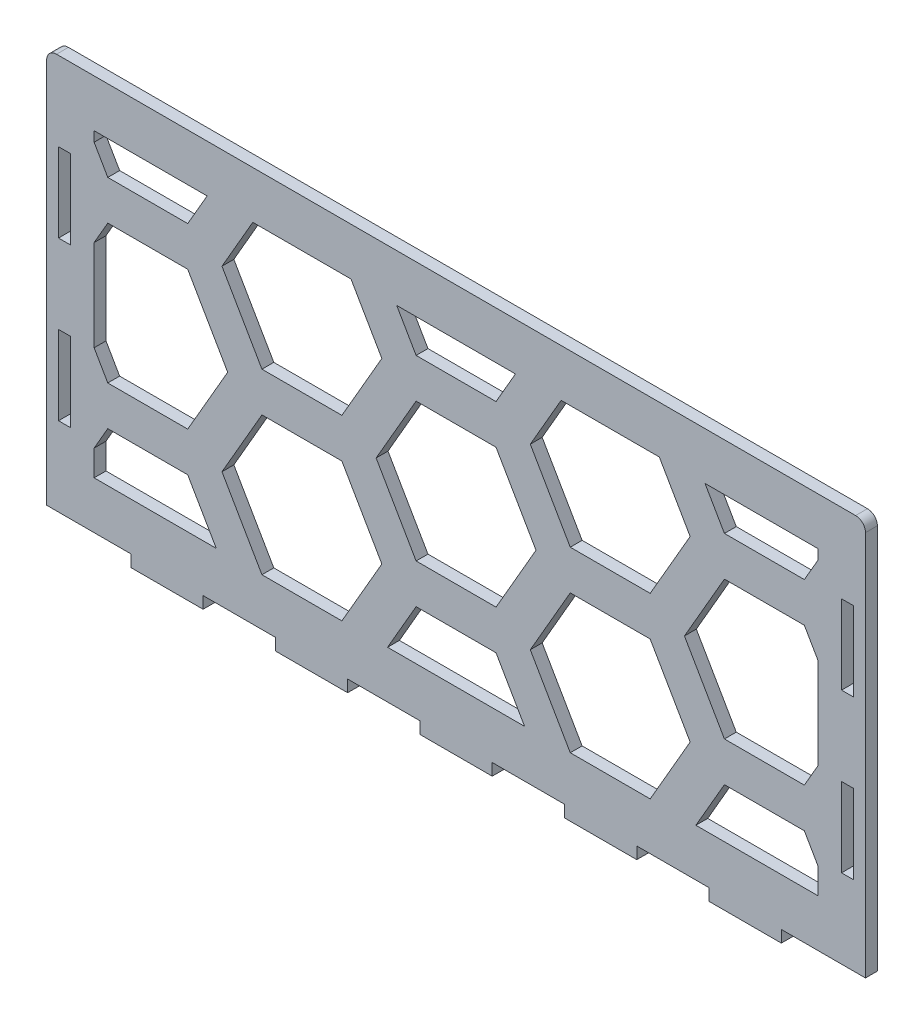
SolidWorks part; units mm, degrees
ref_plane "Front Plane" through (0, 0, 0) normal (0, 0, 1) x (1, 0, 0)
ref_plane "Top Plane" through (0, 0, 0) normal (0, 1, 0) x (1, 0, 0)
ref_plane "Right Plane" through (0, 0, 0) normal (1, 0, 0) x (0, 0, -1)
sketch "Sketch1" plane through (0, 0, 0) normal (0, 0, 1) x (1, 0, 0)
  line L0 (-100.5, -70) -> (-100.5, 70) construction
  line L1 (-103.5, -70) -> (103.5, -70)
  line L2 (-103.5, -70) -> (-103.5, 70)
  line L3 (-103.5, 70) -> (103.5, 70)
  line L4 (103.5, -70) -> (103.5, 70)
  line L5 (-103.5, -70) -> (103.5, 70) construction
  line L6 (-103.5, 70) -> (103.5, -70) construction
  line L7 (100.5, -70) -> (100.5, 70) construction
  line L8 (-63.9545, -73) -> (-45.6818, -73) construction
  line L9 (-9.1364, -73) -> (9.1364, -73)
  line L10 (-9.1364, -73) -> (-9.1364, -70)
  line L11 (-9.1364, -70) -> (9.1364, -70)
  line L12 (9.1364, -73) -> (9.1364, -70)
  line L13 (-9.1364, -73) -> (9.1364, -70) construction
  line L14 (-9.1364, -70) -> (9.1364, -73) construction
  line L15 (27.4091, -73) -> (45.6818, -73)
  line L16 (27.4091, -73) -> (27.4091, -70)
  line L17 (27.4091, -70) -> (45.6818, -70)
  line L18 (45.6818, -73) -> (45.6818, -70)
  line L19 (27.4091, -73) -> (45.6818, -70) construction
  line L20 (27.4091, -70) -> (45.6818, -73) construction
  line L21 (63.9545, -73) -> (82.2273, -73)
  line L22 (63.9545, -73) -> (63.9545, -70)
  line L23 (63.9545, -70) -> (82.2273, -70)
  line L24 (82.2273, -73) -> (82.2273, -70)
  line L25 (63.9545, -73) -> (82.2273, -70) construction
  line L26 (63.9545, -70) -> (82.2273, -73) construction
  line L27 (-45.6818, -73) -> (-27.4091, -73)
  line L28 (-45.6818, -73) -> (-45.6818, -70)
  line L29 (-45.6818, -70) -> (-27.4091, -70)
  line L30 (-27.4091, -73) -> (-27.4091, -70)
  line L31 (-45.6818, -73) -> (-27.4091, -70) construction
  line L32 (-45.6818, -70) -> (-27.4091, -73) construction
  line L33 (-82.2273, -73) -> (-63.9545, -73)
  line L34 (-82.2273, -73) -> (-82.2273, -70)
  line L35 (-82.2273, -70) -> (-63.9545, -70)
  line L36 (-63.9545, -73) -> (-63.9545, -70)
  line L37 (-82.2273, -73) -> (-63.9545, -70) construction
  line L38 (-82.2273, -70) -> (-63.9545, -73) construction
  line L39 (-27.4091, -73) -> (-9.1364, -73) construction
  line L40 (9.1364, -73) -> (27.4091, -73) construction
  line L41 (45.6818, -73) -> (63.9545, -73) construction
  line L42 (82.2273, -73) -> (100.5, -73) construction
  line L43 (-82.2273, -73) -> (-100.5, -73) construction
  line L45 (97.45, 10) -> (100.5, 10)
  line L46 (97.45, 10) -> (97.45, -10)
  line L47 (97.45, -10) -> (100.5, -10)
  line L48 (100.5, 10) -> (100.5, -10)
  line L49 (97.45, 10) -> (100.5, -10) construction
  line L50 (97.45, -10) -> (100.5, 10) construction
  line L51 (97.45, 30) -> (100.5, 30)
  line L52 (97.45, 30) -> (97.45, 50)
  line L53 (97.45, 50) -> (100.5, 50)
  line L54 (100.5, 30) -> (100.5, 50)
  line L55 (97.45, 30) -> (100.5, 50) construction
  line L56 (97.45, 50) -> (100.5, 30) construction
  line L63 (97.45, -30) -> (100.5, -30)
  line L64 (97.45, -30) -> (97.45, -50)
  line L65 (97.45, -50) -> (100.5, -50)
  line L66 (100.5, -30) -> (100.5, -50)
  line L67 (97.45, -30) -> (100.5, -50) construction
  line L68 (97.45, -50) -> (100.5, -30) construction
  line L69 (97.45, 70) -> (97.45, 50) construction
  line L70 (97.45, 30) -> (97.45, 10) construction
  line L71 (97.45, -10) -> (97.45, -30) construction
  line L72 (97.45, -50) -> (97.45, -70) construction
  line L73 (0, -781.5075) -> (0, 49218.4925) construction
  line L78 (-97.45, 50) -> (-100.5, 50)
  line L79 (-100.5, 30) -> (-100.5, 50)
  line L80 (-97.45, 30) -> (-100.5, 30)
  line L81 (-97.45, 30) -> (-97.45, 50)
  line L82 (-97.45, -10) -> (-100.5, -10)
  line L83 (-100.5, 10) -> (-100.5, -10)
  line L84 (-97.45, 10) -> (-100.5, 10)
  line L85 (-97.45, 10) -> (-97.45, -10)
  line L86 (-97.45, -50) -> (-100.5, -50)
  line L87 (-100.5, -30) -> (-100.5, -50)
  line L88 (-97.45, -30) -> (-100.5, -30)
  line L89 (-97.45, -30) -> (-97.45, -50)
  point P0 (0, 0)
  point P10 (0, -71.5)
  point P15 (36.5455, -71.5)
  point P20 (73.0909, -71.5)
  point P25 (-36.5455, -71.5)
  point P30 (-73.0909, -71.5)
  point P35 (98.975, 40)
  point P39 (98.975, 0)
  point P52 (98.975, -40)
  dimension "D1" = 207
  dimension "D2" = 140
  dimension "D5" = 3
  dimension "D6" = 3.05
  dimension "D3" = 3
  dimension "D4" = 3
extrude "Boss-Extrude1" add sketch "Sketch1" along normal blind 3
sketch "Sketch4" plane through (0, 0, 3) normal (0, 0, 1) x (1, 0, 0)
  line L0 (-80, 70) -> (-49.6447, 39.6447)
  line L1 (-103.5, 70) -> (103.5, 70) construction
  line L2 (-14.2893, 25) -> (14.2893, 25)
  line L3 (49.6447, 39.6447) -> (80, 70)
  line L4 (80, 70) -> (-80, 70)
  line L5 (-104.1421, 80) -> (-56.7157, 32.5736)
  line L6 (-14.2893, 15) -> (14.2893, 15)
  line L7 (56.7157, 32.5736) -> (104.1421, 80)
  line L8 (104.1421, 80) -> (-104.1421, 80)
  line L9 (80, 70) -> (103.5, 70)
  line L10 (103.5, 70) -> (103.5, 79.3579)
  line L11 (103.5, -70) -> (103.5, 70) construction
  line L12 (-80, 70) -> (-103.5, 70)
  line L13 (-103.5, 70) -> (-103.5, 79.3579)
  line L14 (-103.5, -70) -> (-103.5, 70) construction
  arc A0 (14.2893, 25) -> (49.6447, 39.6447) centre (14.2893, 75) ccw
  arc A1 (-49.6447, 39.6447) -> (-14.2893, 25) centre (-14.2893, 75) ccw
  arc A2 (-56.7157, 32.5736) -> (-14.2893, 15) centre (-14.2893, 75) ccw
  arc A3 (14.2893, 15) -> (56.7157, 32.5736) centre (14.2893, 75) ccw
  point P4 (0, 25)
  point P10 (35, 25)
  point P13 (-35, 25)
  dimension "D4" = 50
  dimension "D1" = 45
  dimension "D2" = 70
  dimension "D3" = 135
  dimension "D5" = 10
sketch "Sketch5" plane through (0, 0, 3) normal (0, 0, 1) x (1, 0, 0)
  line L0 (-103.5, 70) -> (103.5, 70) construction
  line L1 (-103.5, 70) -> (103.5, 70)
  line L2 (-103.5, 70) -> (-103.5, 30)
  line L3 (-103.5, 30) -> (103.5, 30)
  line L4 (103.5, 70) -> (103.5, 30)
  line L5 (-103.5, 70) -> (103.5, 30) construction
  line L6 (-103.5, 30) -> (103.5, 70) construction
  line L7 (103.5, -70) -> (103.5, 70) construction
  line L8 (97.45, 30) -> (100.5, 30) construction
  point P0 (0, 50)
extrude "Cut-Extrude7" cut sketch "Sketch5" against normal through all both and the other way through all
fillet "Fillet3" radius 2.5 2 edges at (103.5, 30, 1.5) (-103.5, 30, 1.5)
sketch "Sketch6" plane through (0, 0, 0) normal (0, 0, 1) x (1, 0, 0)
  line L0 (-145.7809, -0.5) -> (-165.9882, -0.5)
  line L1 (-145.7809, -45.5) -> (-165.9882, -45.5)
  line L2 (-165.9882, -45.5) -> (-176.0918, -63)
  line L3 (-176.0918, -63) -> (-165.9882, -80.5)
  line L4 (-165.9882, -80.5) -> (-145.7809, -80.5)
  line L5 (-145.7809, -80.5) -> (-135.6773, -63)
  line L6 (-135.6773, -63) -> (-145.7809, -45.5)
  line L13 (-165.9882, -0.5) -> (-176.0918, -18)
  line L14 (-137.1207, -85.5) -> (-127.0171, -103)
  line L15 (-127.0171, -103) -> (-106.8098, -103)
  line L16 (-106.8098, -103) -> (-96.7062, -85.5)
  line L17 (-96.7062, -85.5) -> (-106.8098, -68)
  line L18 (-106.8098, -68) -> (-127.0171, -68)
  line L19 (-127.0171, -68) -> (-137.1207, -85.5)
  line L20 (-176.0918, -18) -> (-165.9882, -35.5)
  line L21 (-165.9882, -35.5) -> (-145.7809, -35.5)
  line L22 (-145.7809, -35.5) -> (-135.6773, -18)
  line L23 (-135.6773, -18) -> (-145.7809, -0.5)
  line L24 (-137.1207, -40.5) -> (-127.0171, -58)
  line L25 (-127.0171, -58) -> (-106.8098, -58)
  line L26 (-106.8098, -58) -> (-96.7062, -40.5)
  line L27 (-96.7062, -40.5) -> (-106.8098, -23)
  line L28 (-106.8098, -23) -> (-127.0171, -23)
  line L29 (-127.0171, -23) -> (-137.1207, -40.5)
  line L30 (-145.7809, 44.5) -> (-165.9882, 44.5)
  line L31 (-165.9882, 44.5) -> (-176.0918, 27)
  line L32 (-176.0918, 27) -> (-165.9882, 9.5)
  line L33 (-165.9882, 9.5) -> (-145.7809, 9.5)
  line L34 (-145.7809, 9.5) -> (-135.6773, 27)
  line L35 (-135.6773, 27) -> (-145.7809, 44.5)
  line L36 (-137.1207, 4.5) -> (-127.0171, -13)
  line L37 (-127.0171, -13) -> (-106.8098, -13)
  line L38 (-106.8098, -13) -> (-96.7062, 4.5)
  line L39 (-96.7062, 4.5) -> (-106.8098, 22)
  line L40 (-106.8098, 22) -> (-127.0171, 22)
  line L41 (-127.0171, 22) -> (-137.1207, 4.5)
  line L42 (-145.7809, 89.5) -> (-165.9882, 89.5)
  line L43 (-165.9882, 89.5) -> (-176.0918, 72)
  line L44 (-176.0918, 72) -> (-165.9882, 54.5)
  line L45 (-165.9882, 54.5) -> (-145.7809, 54.5)
  line L46 (-145.7809, 54.5) -> (-135.6773, 72)
  line L47 (-135.6773, 72) -> (-145.7809, 89.5)
  line L48 (-137.1207, 49.5) -> (-127.0171, 32)
  line L49 (-127.0171, 32) -> (-106.8098, 32)
  line L50 (-106.8098, 32) -> (-96.7062, 49.5)
  line L51 (-96.7062, 49.5) -> (-106.8098, 67)
  line L52 (-106.8098, 67) -> (-127.0171, 67)
  line L53 (-127.0171, 67) -> (-137.1207, 49.5)
  line L54 (-145.7809, 134.5) -> (-165.9882, 134.5)
  line L55 (-165.9882, 134.5) -> (-176.0918, 117)
  line L56 (-176.0918, 117) -> (-165.9882, 99.5)
  line L57 (-165.9882, 99.5) -> (-145.7809, 99.5)
  line L58 (-145.7809, 99.5) -> (-135.6773, 117)
  line L59 (-135.6773, 117) -> (-145.7809, 134.5)
  line L60 (-137.1207, 94.5) -> (-127.0171, 77)
  line L61 (-127.0171, 77) -> (-106.8098, 77)
  line L62 (-106.8098, 77) -> (-96.7062, 94.5)
  line L63 (-96.7062, 94.5) -> (-106.8098, 112)
  line L64 (-106.8098, 112) -> (-127.0171, 112)
  line L65 (-127.0171, 112) -> (-137.1207, 94.5)
  line L66 (-145.7809, 179.5) -> (-165.9882, 179.5)
  line L67 (-165.9882, 179.5) -> (-176.0918, 162)
  line L68 (-176.0918, 162) -> (-165.9882, 144.5)
  line L69 (-165.9882, 144.5) -> (-145.7809, 144.5)
  line L70 (-145.7809, 144.5) -> (-135.6773, 162)
  line L71 (-135.6773, 162) -> (-145.7809, 179.5)
  line L72 (-137.1207, 139.5) -> (-127.0171, 122)
  line L73 (-127.0171, 122) -> (-106.8098, 122)
  line L74 (-106.8098, 122) -> (-96.7062, 139.5)
  line L75 (-96.7062, 139.5) -> (-106.8098, 157)
  line L76 (-106.8098, 157) -> (-127.0171, 157)
  line L77 (-127.0171, 157) -> (-137.1207, 139.5)
  line L102 (-145.7809, -45.5) -> (-145.7809, -0.5) construction
  line L103 (-127.0171, -68) -> (-127.0171, -58) construction
  line L104 (-140.7291, -54.25) -> (-132.0689, -49.25) construction
  line L105 (-59.1784, 139.5) -> (-49.0748, 122)
  line L106 (-49.0748, 122) -> (-28.8675, 122)
  line L107 (-28.8675, 122) -> (-18.7639, 139.5)
  line L108 (-18.7639, 139.5) -> (-28.8675, 157)
  line L109 (-28.8675, 157) -> (-49.0748, 157)
  line L110 (-49.0748, 157) -> (-59.1784, 139.5)
  line L111 (-67.8387, 179.5) -> (-88.0459, 179.5)
  line L112 (-88.0459, 179.5) -> (-98.1495, 162)
  line L113 (-98.1495, 162) -> (-88.0459, 144.5)
  line L114 (-88.0459, 144.5) -> (-67.8387, 144.5)
  line L115 (-67.8387, 144.5) -> (-57.735, 162)
  line L116 (-57.735, 162) -> (-67.8387, 179.5)
  line L117 (-67.8387, 134.5) -> (-88.0459, 134.5)
  line L118 (-88.0459, 134.5) -> (-98.1495, 117)
  line L119 (-98.1495, 117) -> (-88.0459, 99.5)
  line L120 (-88.0459, 99.5) -> (-67.8387, 99.5)
  line L121 (-67.8387, 99.5) -> (-57.735, 117)
  line L122 (-57.735, 117) -> (-67.8387, 134.5)
  line L123 (-67.8387, 89.5) -> (-88.0459, 89.5)
  line L124 (-88.0459, 89.5) -> (-98.1495, 72)
  line L125 (-98.1495, 72) -> (-88.0459, 54.5)
  line L126 (-88.0459, 54.5) -> (-67.8387, 54.5)
  line L127 (-67.8387, 54.5) -> (-57.735, 72)
  line L128 (-57.735, 72) -> (-67.8387, 89.5)
  line L129 (-67.8387, 44.5) -> (-88.0459, 44.5)
  line L130 (-88.0459, 44.5) -> (-98.1495, 27)
  line L131 (-98.1495, 27) -> (-88.0459, 9.5)
  line L132 (-88.0459, 9.5) -> (-67.8387, 9.5)
  line L133 (-67.8387, 9.5) -> (-57.735, 27)
  line L134 (-57.735, 27) -> (-67.8387, 44.5)
  line L135 (-59.1784, 4.5) -> (-49.0748, -13)
  line L136 (-49.0748, -13) -> (-28.8675, -13)
  line L137 (-28.8675, -13) -> (-18.7639, 4.5)
  line L138 (-18.7639, 4.5) -> (-28.8675, 22)
  line L139 (-28.8675, 22) -> (-49.0748, 22)
  line L140 (-49.0748, 22) -> (-59.1784, 4.5)
  line L141 (-67.8387, -0.5) -> (-88.0459, -0.5)
  line L142 (-88.0459, -0.5) -> (-98.1495, -18)
  line L143 (-98.1495, -18) -> (-88.0459, -35.5)
  line L144 (-88.0459, -35.5) -> (-67.8387, -35.5)
  line L145 (-67.8387, -35.5) -> (-57.735, -18)
  line L146 (-57.735, -18) -> (-67.8387, -0.5)
  line L147 (-59.1784, -40.5) -> (-49.0748, -58)
  line L148 (-49.0748, -58) -> (-28.8675, -58)
  line L149 (-28.8675, -58) -> (-18.7639, -40.5)
  line L150 (-18.7639, -40.5) -> (-28.8675, -23)
  line L151 (-28.8675, -23) -> (-49.0748, -23)
  line L152 (-49.0748, -23) -> (-59.1784, -40.5)
  line L153 (-67.8387, -45.5) -> (-88.0459, -45.5)
  line L154 (-88.0459, -45.5) -> (-98.1495, -63)
  line L155 (-98.1495, -63) -> (-88.0459, -80.5)
  line L156 (-88.0459, -80.5) -> (-67.8387, -80.5)
  line L157 (-67.8387, -80.5) -> (-57.735, -63)
  line L158 (-57.735, -63) -> (-67.8387, -45.5)
  line L159 (-59.1784, -85.5) -> (-49.0748, -103)
  line L160 (-49.0748, -103) -> (-28.8675, -103)
  line L161 (-28.8675, -103) -> (-18.7639, -85.5)
  line L162 (-18.7639, -85.5) -> (-28.8675, -68)
  line L163 (-28.8675, -68) -> (-49.0748, -68)
  line L164 (-49.0748, -68) -> (-59.1784, -85.5)
  line L165 (-59.1784, 49.5) -> (-49.0748, 32)
  line L166 (-49.0748, 32) -> (-28.8675, 32)
  line L167 (-28.8675, 32) -> (-18.7639, 49.5)
  line L168 (-18.7639, 49.5) -> (-28.8675, 67)
  line L169 (-28.8675, 67) -> (-49.0748, 67)
  line L170 (-49.0748, 67) -> (-59.1784, 49.5)
  line L171 (-59.1784, 94.5) -> (-49.0748, 77)
  line L172 (-49.0748, 77) -> (-28.8675, 77)
  line L173 (-28.8675, 77) -> (-18.7639, 94.5)
  line L174 (-18.7639, 94.5) -> (-28.8675, 112)
  line L175 (-28.8675, 112) -> (-49.0748, 112)
  line L176 (-49.0748, 112) -> (-59.1784, 94.5)
  line L177 (18.7639, 139.5) -> (28.8675, 122)
  line L178 (28.8675, 122) -> (49.0748, 122)
  line L179 (49.0748, 122) -> (59.1784, 139.5)
  line L180 (59.1784, 139.5) -> (49.0748, 157)
  line L181 (49.0748, 157) -> (28.8675, 157)
  line L182 (28.8675, 157) -> (18.7639, 139.5)
  line L183 (10.1036, 179.5) -> (-10.1036, 179.5)
  line L184 (-10.1036, 179.5) -> (-20.2073, 162)
  line L185 (-20.2073, 162) -> (-10.1036, 144.5)
  line L186 (-10.1036, 144.5) -> (10.1036, 144.5)
  line L187 (10.1036, 144.5) -> (20.2073, 162)
  line L188 (20.2073, 162) -> (10.1036, 179.5)
  line L189 (10.1036, 134.5) -> (-10.1036, 134.5)
  line L190 (-10.1036, 134.5) -> (-20.2073, 117)
  line L191 (-20.2073, 117) -> (-10.1036, 99.5)
  line L192 (-10.1036, 99.5) -> (10.1036, 99.5)
  line L193 (10.1036, 99.5) -> (20.2073, 117)
  line L194 (20.2073, 117) -> (10.1036, 134.5)
  line L195 (10.1036, 89.5) -> (-10.1036, 89.5)
  line L196 (-10.1036, 89.5) -> (-20.2073, 72)
  line L197 (-20.2073, 72) -> (-10.1036, 54.5)
  line L198 (-10.1036, 54.5) -> (10.1036, 54.5)
  line L199 (10.1036, 54.5) -> (20.2073, 72)
  line L200 (20.2073, 72) -> (10.1036, 89.5)
  line L201 (10.1036, 44.5) -> (-10.1036, 44.5)
  line L202 (-10.1036, 44.5) -> (-20.2073, 27)
  line L203 (-20.2073, 27) -> (-10.1036, 9.5)
  line L204 (-10.1036, 9.5) -> (10.1036, 9.5)
  line L205 (10.1036, 9.5) -> (20.2073, 27)
  line L206 (20.2073, 27) -> (10.1036, 44.5)
  line L207 (18.7639, 4.5) -> (28.8675, -13)
  line L208 (28.8675, -13) -> (49.0748, -13)
  line L209 (49.0748, -13) -> (59.1784, 4.5)
  line L210 (59.1784, 4.5) -> (49.0748, 22)
  line L211 (49.0748, 22) -> (28.8675, 22)
  line L212 (28.8675, 22) -> (18.7639, 4.5)
  line L213 (10.1036, -0.5) -> (-10.1036, -0.5)
  line L214 (-10.1036, -0.5) -> (-20.2073, -18)
  line L215 (-20.2073, -18) -> (-10.1036, -35.5)
  line L216 (-10.1036, -35.5) -> (10.1036, -35.5)
  line L217 (10.1036, -35.5) -> (20.2073, -18)
  line L218 (20.2073, -18) -> (10.1036, -0.5)
  line L219 (18.7639, -40.5) -> (28.8675, -58)
  line L220 (28.8675, -58) -> (49.0748, -58)
  line L221 (49.0748, -58) -> (59.1784, -40.5)
  line L222 (59.1784, -40.5) -> (49.0748, -23)
  line L223 (49.0748, -23) -> (28.8675, -23)
  line L224 (28.8675, -23) -> (18.7639, -40.5)
  line L225 (10.1036, -45.5) -> (-10.1036, -45.5)
  line L226 (-10.1036, -45.5) -> (-20.2073, -63)
  line L227 (-20.2073, -63) -> (-10.1036, -80.5)
  line L228 (-10.1036, -80.5) -> (10.1036, -80.5)
  line L229 (10.1036, -80.5) -> (20.2073, -63)
  line L230 (20.2073, -63) -> (10.1036, -45.5)
  line L231 (18.7639, -85.5) -> (28.8675, -103)
  line L232 (28.8675, -103) -> (49.0748, -103)
  line L233 (49.0748, -103) -> (59.1784, -85.5)
  line L234 (59.1784, -85.5) -> (49.0748, -68)
  line L235 (49.0748, -68) -> (28.8675, -68)
  line L236 (28.8675, -68) -> (18.7639, -85.5)
  line L237 (18.7639, 49.5) -> (28.8675, 32)
  line L238 (28.8675, 32) -> (49.0748, 32)
  line L239 (49.0748, 32) -> (59.1784, 49.5)
  line L240 (59.1784, 49.5) -> (49.0748, 67)
  line L241 (49.0748, 67) -> (28.8675, 67)
  line L242 (28.8675, 67) -> (18.7639, 49.5)
  line L243 (18.7639, 94.5) -> (28.8675, 77)
  line L244 (28.8675, 77) -> (49.0748, 77)
  line L245 (49.0748, 77) -> (59.1784, 94.5)
  line L246 (59.1784, 94.5) -> (49.0748, 112)
  line L247 (49.0748, 112) -> (28.8675, 112)
  line L248 (28.8675, 112) -> (18.7639, 94.5)
  line L249 (96.7062, 139.5) -> (106.8098, 122)
  line L250 (106.8098, 122) -> (127.0171, 122)
  line L251 (127.0171, 122) -> (137.1207, 139.5)
  line L252 (137.1207, 139.5) -> (127.0171, 157)
  line L253 (127.0171, 157) -> (106.8098, 157)
  line L254 (106.8098, 157) -> (96.7062, 139.5)
  line L255 (88.0459, 179.5) -> (67.8387, 179.5)
  line L256 (67.8387, 179.5) -> (57.735, 162)
  line L257 (57.735, 162) -> (67.8387, 144.5)
  line L258 (67.8387, 144.5) -> (88.0459, 144.5)
  line L259 (88.0459, 144.5) -> (98.1495, 162)
  line L260 (98.1495, 162) -> (88.0459, 179.5)
  line L261 (88.0459, 134.5) -> (67.8387, 134.5)
  line L262 (67.8387, 134.5) -> (57.735, 117)
  line L263 (57.735, 117) -> (67.8387, 99.5)
  line L264 (67.8387, 99.5) -> (88.0459, 99.5)
  line L265 (88.0459, 99.5) -> (98.1495, 117)
  line L266 (98.1495, 117) -> (88.0459, 134.5)
  line L267 (88.0459, 89.5) -> (67.8387, 89.5)
  line L268 (67.8387, 89.5) -> (57.735, 72)
  line L269 (57.735, 72) -> (67.8387, 54.5)
  line L270 (67.8387, 54.5) -> (88.0459, 54.5)
  line L271 (88.0459, 54.5) -> (98.1495, 72)
  line L272 (98.1495, 72) -> (88.0459, 89.5)
  line L273 (88.0459, 44.5) -> (67.8387, 44.5)
  line L274 (67.8387, 44.5) -> (57.735, 27)
  line L275 (57.735, 27) -> (67.8387, 9.5)
  line L276 (67.8387, 9.5) -> (88.0459, 9.5)
  line L277 (88.0459, 9.5) -> (98.1495, 27)
  line L278 (98.1495, 27) -> (88.0459, 44.5)
  line L279 (96.7062, 4.5) -> (106.8098, -13)
  line L280 (106.8098, -13) -> (127.0171, -13)
  line L281 (127.0171, -13) -> (137.1207, 4.5)
  line L282 (137.1207, 4.5) -> (127.0171, 22)
  line L283 (127.0171, 22) -> (106.8098, 22)
  line L284 (106.8098, 22) -> (96.7062, 4.5)
  line L285 (88.0459, -0.5) -> (67.8387, -0.5)
  line L286 (67.8387, -0.5) -> (57.735, -18)
  line L287 (57.735, -18) -> (67.8387, -35.5)
  line L288 (67.8387, -35.5) -> (88.0459, -35.5)
  line L289 (88.0459, -35.5) -> (98.1495, -18)
  line L290 (98.1495, -18) -> (88.0459, -0.5)
  line L291 (96.7062, -40.5) -> (106.8098, -58)
  line L292 (106.8098, -58) -> (127.0171, -58)
  line L293 (127.0171, -58) -> (137.1207, -40.5)
  line L294 (137.1207, -40.5) -> (127.0171, -23)
  line L295 (127.0171, -23) -> (106.8098, -23)
  line L296 (106.8098, -23) -> (96.7062, -40.5)
  line L297 (88.0459, -45.5) -> (67.8387, -45.5)
  line L298 (67.8387, -45.5) -> (57.735, -63)
  line L299 (57.735, -63) -> (67.8387, -80.5)
  line L300 (67.8387, -80.5) -> (88.0459, -80.5)
  line L301 (88.0459, -80.5) -> (98.1495, -63)
  line L302 (98.1495, -63) -> (88.0459, -45.5)
  line L303 (96.7062, -85.5) -> (106.8098, -103)
  line L304 (106.8098, -103) -> (127.0171, -103)
  line L305 (127.0171, -103) -> (137.1207, -85.5)
  line L306 (137.1207, -85.5) -> (127.0171, -68)
  line L307 (127.0171, -68) -> (106.8098, -68)
  line L308 (106.8098, -68) -> (96.7062, -85.5)
  line L309 (96.7062, 49.5) -> (106.8098, 32)
  line L310 (106.8098, 32) -> (127.0171, 32)
  line L311 (127.0171, 32) -> (137.1207, 49.5)
  line L312 (137.1207, 49.5) -> (127.0171, 67)
  line L313 (127.0171, 67) -> (106.8098, 67)
  line L314 (106.8098, 67) -> (96.7062, 49.5)
  line L315 (96.7062, 94.5) -> (106.8098, 77)
  line L316 (106.8098, 77) -> (127.0171, 77)
  line L317 (127.0171, 77) -> (137.1207, 94.5)
  line L318 (137.1207, 94.5) -> (127.0171, 112)
  line L319 (127.0171, 112) -> (106.8098, 112)
  line L320 (106.8098, 112) -> (96.7062, 94.5)
  line L321 (-137.1207, 139.5) -> (-59.1784, 139.5) construction
  line L322 (-93.0977, -54.25) -> (-101.758, -49.25) construction
  line L324 (-91.5, -58) -> (91.5, -58)
  line L325 (-91.5, -58) -> (-91.5, 58)
  line L326 (-91.5, 58) -> (91.5, 58)
  line L327 (91.5, -58) -> (91.5, 58)
  line L328 (-91.5, -58) -> (91.5, 58) construction
  line L329 (-91.5, 58) -> (91.5, -58) construction
  line L331 (-106.8098, -23) -> (-91.5, -23) construction
  line L332 (106.8098, -23) -> (91.5, -23) construction
  line L333 (-91.5, 18) -> (91.5, 18)
  line L335 (101, 30) -> (-101, 30) construction
  line L336 (103.5, -70) -> (103.5, 27.5) construction
  line L337 (9.1364, -70) -> (27.4091, -70) construction
  circle A0 centre (-155.8846, -63) radius 17.5 construction
  circle A1 centre (-116.9134, -85.5) radius 17.5 construction
  point P10 (-127.0171, -63)
  point P301 (0, 0)
  dimension "D3" = 35
  dimension "D2" = 45
  dimension "D5" = 12
  dimension "D6" = 12
  dimension "D7" = 12
  dimension "D1" = 6
  dimension "D4" = 4
extrude "Cut-Extrude8" cut sketch "Sketch6" against normal through all both and the other way through all contours L325 L143 L144 L145 L146 L141 L142 | L333 L325 L131 L132 L133 | L333 L140 L135 L136 L137 L138 | L217 L218 L213 L214 L215 L216 | L333 L212 L207 L208 L209 L210 | L289 L327 L290 L285 L286 L287 L288 | L333 L275 L276 L277 L327 | L333 L203 L204 L205 | L151 L152 L147 L148 L149 L150 | L325 L324 L158 L153 L154 | L226 L324 L230 L225 | L223 L224 L219 L220 L221 L222 | L324 L327 L302 L297 L298
